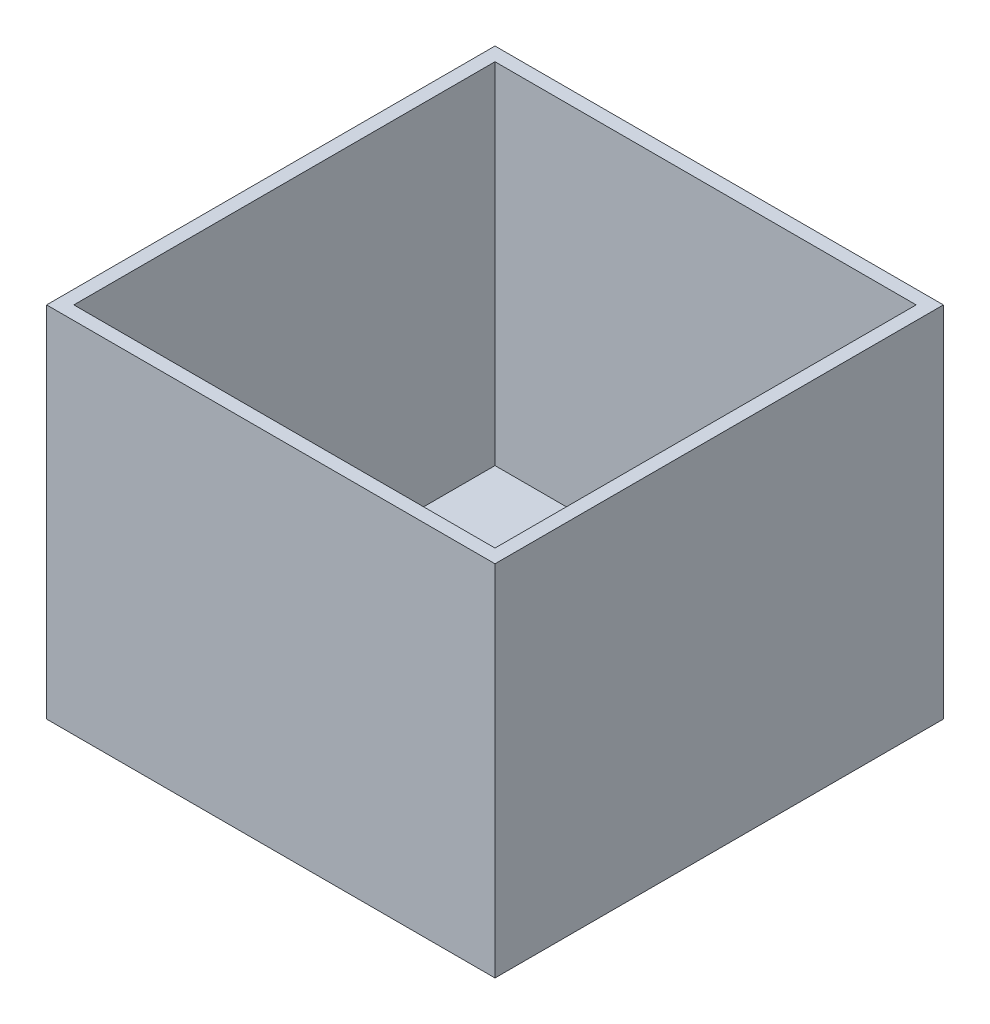
SolidWorks part; units mm, degrees
ref_plane "Front Plane" through (0, 0, 0) normal (0, 0, 1) x (1, 0, 0)
ref_plane "Top Plane" through (0, 0, 0) normal (0, 1, 0) x (1, 0, 0)
ref_plane "Right Plane" through (0, 0, 0) normal (1, 0, 0) x (0, 0, -1)
sketch "Sketch1" plane through (0, 0, 0) normal (0, 1, 0) x (1, 0, 0)
  line L1 (-250, 250) -> (250, 250)
  line L2 (-250, 250) -> (-250, -250)
  line L3 (-250, -250) -> (250, -250)
  line L4 (250, 250) -> (250, -250)
  line L5 (-250, 250) -> (250, -250) construction
  line L6 (-250, -250) -> (250, 250) construction
  point P0 (0, 0)
  dimension "D1" = 500
  dimension "D2" = 500
extrude "Boss-Extrude1" add sketch "Sketch1" along normal blind 10
sketch "Sketch2" plane through (0, 0, 0) normal (0, 1, 0) x (1, 0, 0)
  line L0 (250, 250) -> (-250, 250) construction
  line L1 (-250, -250) -> (250, -250)
  line L2 (-250, -250) -> (-250, 250)
  line L3 (-250, 250) -> (250, 250)
  line L4 (250, -250) -> (250, 250)
  line L5 (-250, -250) -> (250, 250) construction
  line L6 (-250, 250) -> (250, -250) construction
  line L8 (-234.8072, -234.8072) -> (234.8072, -234.8072)
  line L9 (-234.8072, -234.8072) -> (-234.8072, 234.8072)
  line L10 (-234.8072, 234.8072) -> (234.8072, 234.8072)
  line L11 (234.8072, -234.8072) -> (234.8072, 234.8072)
  line L12 (-234.8072, -234.8072) -> (234.8072, 234.8072) construction
  line L13 (-234.8072, 234.8072) -> (234.8072, -234.8072) construction
  point P0 (0, 0)
  point P8 (0, 0)
  point P13 (234.8072, 234.8072)
extrude "Boss-Extrude2" add sketch "Sketch2" along normal blind 400
sketch3d "URDF Reference"
  line L0 (0, 0, 0) -> (10, 0, 0) construction
  line L1 (0, 0, 0) -> (0, 0, -10) construction
  point P0 (0, 0, 0)
  point P1 (0, 0, 0)
